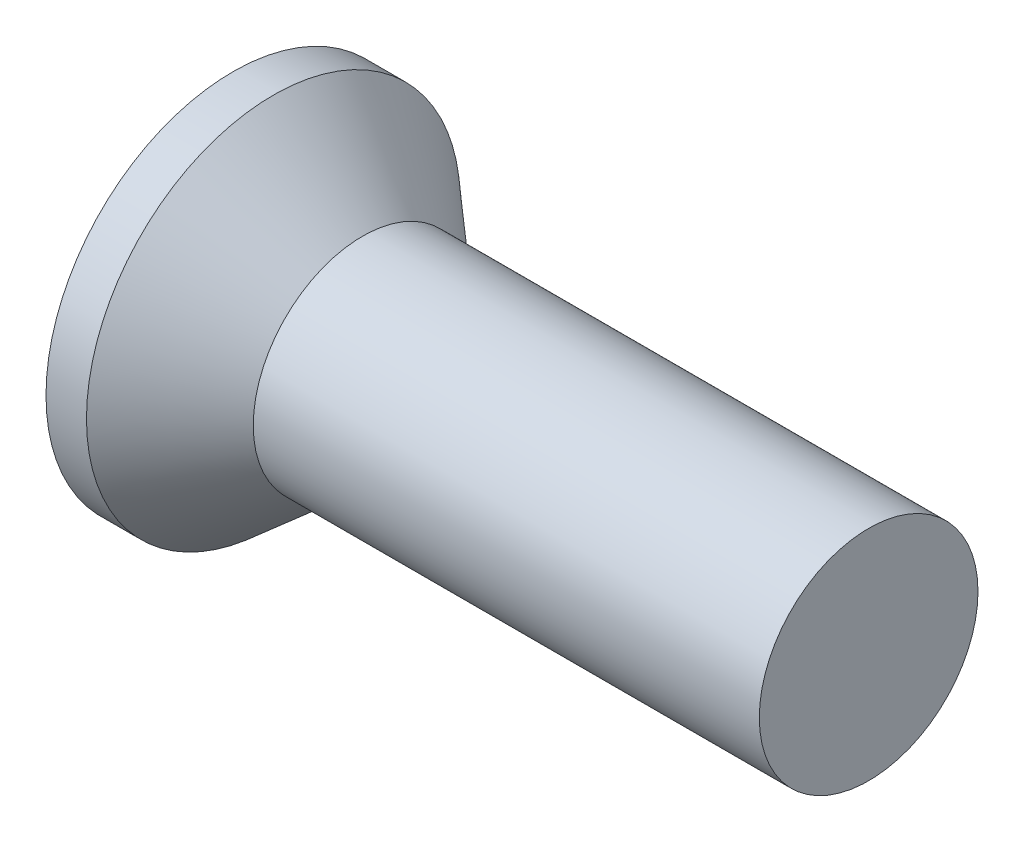
SolidWorks part; units mm, degrees
revolve "Base-Revolve" add sketch "BodySke" angle 360 about L5
sketch "BodySke" plane through (0, 0, 0) normal (0, 0, 1) x (1, 0, 0)
  line L0 (0, 0) -> (0, 1.8669)
  line L1 (0, 1.8669) -> (0.4042, 1.8669)
  line L2 (1.2954, 1.0922) -> (6.35, 1.0922)
  line L3 (6.35, 1.0922) -> (6.35, 0)
  line L4 (6.35, 0) -> (0, 0)
  line L5 (-6.35, 0) -> (82.55, 0) construction
  line L6 (1.2954, -1.0922) -> (6.35, -1.0922) construction
  line L7 (0.4042, -1.8669) -> (1.2954, -1.0922) construction
  line L8 (0.4042, 1.8669) -> (1.2954, 1.0922)
  line L9 (0, -1.8669) -> (0.4042, -1.8669) construction
  line L10 (1.7501, 2.6797) -> (1.7501, -6.8453) construction
  line L11 (0, 6.35) -> (0, -3.175) construction
  dimension "Diameter" = 2.1844
  dimension "Length" = 6.35
  dimension "Head_ht" = 1.2954
  dimension "Head_dia" = 3.7338
  dimension "Head_ang" = 82
  dimension "D6" = 0.4042
  dimension "Advance" = 0.4547
  dimension "Thread_nom" = 6.35
cosmetic thread "ThreadCosmetic" [suppressed] parameters "Thread_length"=4.5999, "Thread_minor"=1.6459
extrude "Slot" [suppressed] cut sketch "Sketch2" against normal blind 0.508
sketch "Sketch2" plane through (0, 0, 0) normal (-1, 0, 0) x (0, 0, 1)
  line L0 (-1.8669, -0.3937) -> (1.8669, -0.3937)
  line L1 (-1.8669, -0.3937) -> (-1.8669, 0.3937)
  line L2 (1.8669, 0.3937) -> (-1.8669, 0.3937)
  line L3 (1.8669, 0.3937) -> (1.8669, -0.3937)
  dimension "Slot_width" = 0.7874
  dimension "D1" = 0.3937
  dimension "D2" = 3.7338
  dimension "D3" = 1.8669
ref_plane "Plane1" through (0, 0, 0) normal (0, 0, 1) x (1, 0, 0)
ref_plane "Plane2" through (0, 0, 0) normal (0, 1, 0) x (1, 0, 0)
ref_plane "Plane3" through (0, 0, 0) normal (1, 0, 0) x (0, 0, -1)
sketch "Sketch3" plane through (0, 0, 0) normal (-1, 0, 0) x (0, 0, 1)
  line L0 (-0.3429, 1.524) -> (0.3429, 1.524)
  line L1 (0.3429, 1.524) -> (0.3429, -1.524)
  line L2 (0.3429, -1.524) -> (-0.3429, -1.524)
  line L3 (-0.3429, -1.524) -> (-0.3429, 1.524)
  dimension "Cross_dia" = 3.048
  dimension "Cross_width" = 0.6858
  dimension "D1" = 1.524
  dimension "D2" = 0.3429
ref_plane "Plane4" through (1.6764, 0, 0) normal (-1, 0, 0) x (0, 0, 1)
sketch "Sketch4" plane through (1.6764, 0, 0) normal (-1, 0, 0) x (0, 0, 1)
  line L0 (-0.1714, 0.1714) -> (0.1714, 0.1715)
  line L3 (0.1714, 0.1715) -> (0.1715, -0.1714)
  line L4 (0.1715, -0.1714) -> (-0.1714, -0.1715)
  line L5 (-0.1714, -0.1715) -> (-0.1714, 0.1714)
  dimension "D2" = 0.3429
  dimension "D1" = 0.3429
  dimension "D3" = 0.1714
  dimension "D4" = 0.1714
loft "Cross" cut profiles "Sketch3", "Sketch4"
pattern_circular "CirPattern1" count 2 every 90 about axis through (0, 0, 0) along (1, 0, 0) of "Cross"
sketch "ThdSchSke" plane through (0, 0, 0) normal (0, 0, 1) x (1, 0, 0)
  line L0 (1.7501, -0.823) -> (1.5616, -1.0922)
  line L1 (1.7501, -0.823) -> (1.9386, -1.0922)
  line L2 (1.9386, -1.0922) -> (1.9386, -1.3652)
  line L3 (-3.175, 0) -> (5.1513, 0) construction
  line L5 (1.9386, -1.3652) -> (1.5616, -1.3652)
  line L6 (1.5616, -1.3652) -> (1.5616, -1.0922)
  line L7 (0, 1.8669) -> (0, -1.8669) construction
  dimension "Diameter" = 2.1844
  dimension "Thread_minor" = 1.6459
  dimension "Start" = 1.7501
revolve "ThreadSchematic" [suppressed] cut sketch "ThdSchSke" angle 360 about L3
pattern_linear "ThdSchPat" [suppressed]
equation "\"D1@Sketch3\" = \"Cross_dia@Sketch3\" / 2"
equation "\"D2@Sketch3\" = \"Cross_width@Sketch3\" / 2"
equation "\"D1@Sketch4\" = \"Cross_width@Sketch3\" *.5"
equation "\"D2@Sketch4\" = \"D1@Sketch4\""
equation "\"D4@Sketch4\" = \"D2@Sketch4\" / 2"
equation "\"D3@Sketch4\" = \"D1@Sketch4\" / 2"
equation "\"D1@Sketch2\" = \"Slot_width@Sketch2\" / 2"
equation "\"D2@Sketch2\" = \"Head_dia@BodySke\""
equation "\"D3@Sketch2\" = \"D2@Sketch2\" / 2"
equation "\"Thread_length@ThreadCosmetic\" = ((sgn( (\"Length@BodySke\" - \"Advance@BodySke\" - \"Head_ht@BodySke\" ) - \"Thread_nom@BodySke\" )-1)*( (\"Length@BodySke\" - \"Advance@BodySke\" - \"Head_ht@BodySke\" ) - \"Thread_nom@BodySke\" ))/-2+ \"Thread_nom@BodySke\""
equation "\"Thread_minor@ThdSchSke\" = \"Thread_minor@ThreadCosmetic\""
equation "\"Diameter@ThdSchSke\" = \"Diameter@BodySke\""
equation "\"Overcut@ThdSchSke\" = \"Diameter@BodySke\" * 1.25"
equation "\"Start@ThdSchSke\" = 0.000001 + \"Length@BodySke\" - \"Thread_length@ThreadCosmetic\"  '---Countersunk---"
equation "\"Num_threads@ThdSchPat\" = int( \"Thread_length@ThreadCosmetic\" / \"Advance@BodySke\" + 0.999 )  + 1"
equation "\"Advance@ThdSchPat\" = \"Thread_length@ThreadCosmetic\" /  (\"Num_threads@ThdSchPat\" - 1) 'relax it"
